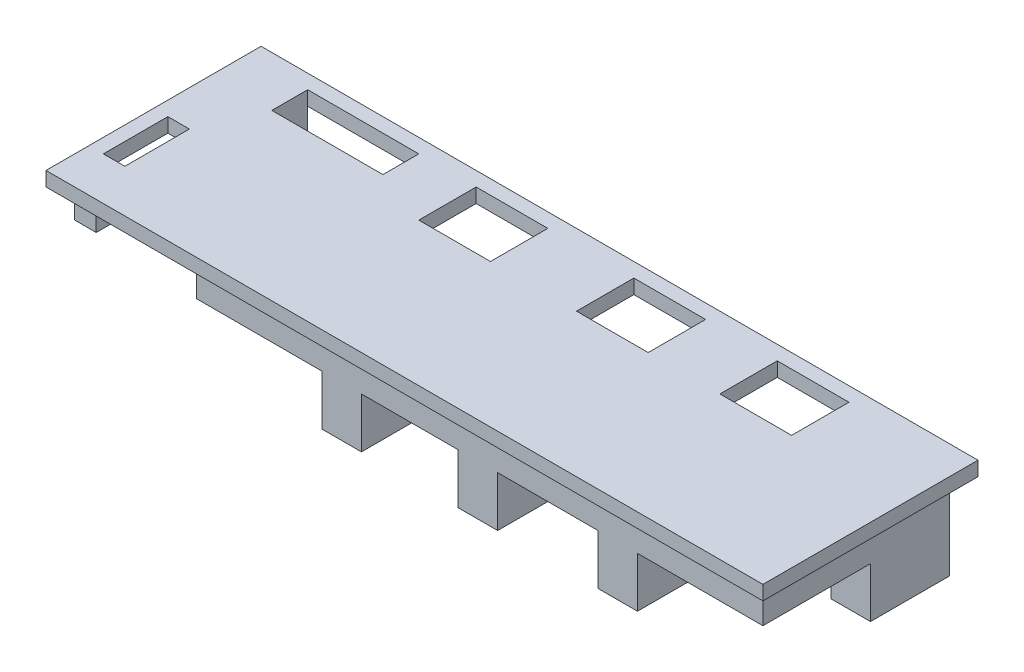
SolidWorks part; units mm, degrees
ref_plane "Front Plane" through (0, 0, 0) normal (0, 0, 1) x (1, 0, 0)
ref_plane "Top Plane" through (0, 0, 0) normal (0, 1, 0) x (1, 0, 0)
ref_plane "Right Plane" through (0, 0, 0) normal (1, 0, 0) x (0, 0, -1)
sketch "Sketch1" plane through (0, 0, 0) normal (0, 1, 0) x (1, 0, 0)
  line L0 (2, 28) -> (98, 28)
  line L1 (0, 0) -> (100, 0)
  line L2 (0, 0) -> (0, 30)
  line L3 (0, 30) -> (100, 30)
  line L4 (100, 0) -> (100, 30)
  line L5 (98, 2) -> (98, 28)
  line L6 (2, 2) -> (98, 2)
  line L7 (2, 2) -> (2, 28)
  line L8 (98, 20) -> (2, 20)
  line L9 (84, 28) -> (84, 20)
  line L10 (74, 28) -> (74, 20)
  line L11 (64, 28) -> (64, 20)
  line L12 (54, 28) -> (54, 20)
  line L13 (42, 28) -> (42, 20)
  line L14 (32, 28) -> (32, 20)
  line L15 (24, 28) -> (24, 20)
  line L16 (24, 23) -> (8.5, 23)
  line L17 (8.5, 23) -> (8.5, 28)
  line L18 (2, 6) -> (5, 6)
  line L19 (5, 6) -> (5, 15)
  line L20 (5, 15) -> (2, 15)
  dimension "D1" = 2
  dimension "D2" = 8
  dimension "D3" = 14
  dimension "D4" = 10
  dimension "D5" = 10
  dimension "D6" = 10
  dimension "D7" = 12
  dimension "D8" = 10
  dimension "D9" = 8
  dimension "D10" = 3
  dimension "D11" = 6.5
  dimension "D12" = 4
extrude "Boss-Extrude3" add sketch "Sketch1" against normal blind 2 contours L1 L4 L3 L2 L6 L7 L0 L5 | L5 L8 L7 L6 | L0 L9 L8 L5 | L0 L11 L8 L10 | L0 L13 L8 L12 | L0 L15 L8 L14 | L16 L17 L0 L7 L8 L15
sketch "Sketch2" plane through (0, -2, 0) normal (0, -1, 0) x (1, 0, 0)
  line L0 (100, 0) -> (100, -30) construction
  line L1 (0, 0) -> (100, 0)
  line L2 (0, 0) -> (0, -30)
  line L3 (0, -30) -> (100, -30)
  line L4 (100, 0) -> (100, -30)
  line L5 (0, -30) -> (100, -30) construction
  line L6 (2, -2) -> (2, -28)
  line L7 (2, -28) -> (98, -28)
  line L8 (98, -2) -> (98, -28)
  line L9 (2, -2) -> (98, -2)
  line L10 (98, -17) -> (92.5, -17)
  line L11 (92.5, -17) -> (92.5, -28)
  dimension "D1" = 2
extrude "Boss-Extrude4" add sketch "Sketch2" along normal blind 12 contours L10 L11 L7 L8
sketch "Sketch3" plane through (0, -2, 0) normal (0, -1, 0) x (1, 0, 0)
  line L0 (8.5, -28) -> (2, -28)
  line L1 (0, 0) -> (0, -30) construction
  line L2 (2, -28) -> (2, -17)
  line L3 (2, -17) -> (24, -17)
  line L4 (24, -17) -> (24, -23)
  line L5 (24, -23) -> (8.5, -23)
  line L6 (8.5, -23) -> (8.5, -28)
  line M7 (8.5, -28) -> (8.5, -23)
  line M8 (8.5, -23) -> (24, -23)
  dimension "D1" = 2
extrude "Boss-Extrude5" add sketch "Sketch3" along normal blind 9.5 contours L4 L3 L2 L0 M7 M8
sketch "Sketch9" plane through (0, -2, 0) normal (0, -1, 0) x (1, 0, 0)
  line L0 (0, 0) -> (100, 0) construction
  line L1 (2, -2) -> (5, -2)
  line L2 (2, -2) -> (2, -5)
  line L3 (2, -5) -> (5, -5)
  line L4 (5, -2) -> (5, -5)
  line L5 (0, 0) -> (0, -30) construction
  dimension "D1" = 2
  dimension "D2" = 2
extrude "Boss-Extrude17" add sketch "Sketch9" along normal blind 4
sketch "Sketch12" plane through (0, -2, 0) normal (0, -1, 0) x (1, 0, 0)
  line L0 (0, 0) -> (100, 0) construction
  line L1 (19, -17) -> (98, -17)
  line L2 (19, -17) -> (19, -2)
  line L3 (19, -2) -> (98, -2)
  line L4 (98, -17) -> (98, -2)
  dimension "D1" = 2
  dimension "D2" = 0
extrude "Boss-Extrude22" add sketch "Sketch12" along normal blind 5
sketch "Sketch13" plane through (0, -7, 0) normal (0, -1, 0) x (1, 0, 0)
  line L0 (98, -17) -> (98, -2) construction
  line L1 (98, -2) -> (19, -2) construction
  line L2 (42, -2) -> (36.5, -2)
  line L3 (61, -2) -> (55.5, -2)
  line L4 (80.5, -2) -> (75, -2)
  line L5 (80.5, -2) -> (80.5, -15)
  line L6 (80.5, -15) -> (75, -15)
  line L7 (75, -2) -> (75, -15)
  line L8 (61, -2) -> (61, -15)
  line L9 (61, -15) -> (55.5, -15)
  line L10 (55.5, -2) -> (55.5, -15)
  line L11 (42, -2) -> (42, -15)
  line L12 (42, -15) -> (36.5, -15)
  line L13 (36.5, -2) -> (36.5, -15)
  line L14 (98, -2) -> (19, -2) construction
  dimension "D1" = 17.5
  dimension "D2" = 37
  dimension "D3" = 56
extrude "Boss-Extrude23" add sketch "Sketch13" along normal blind 7
